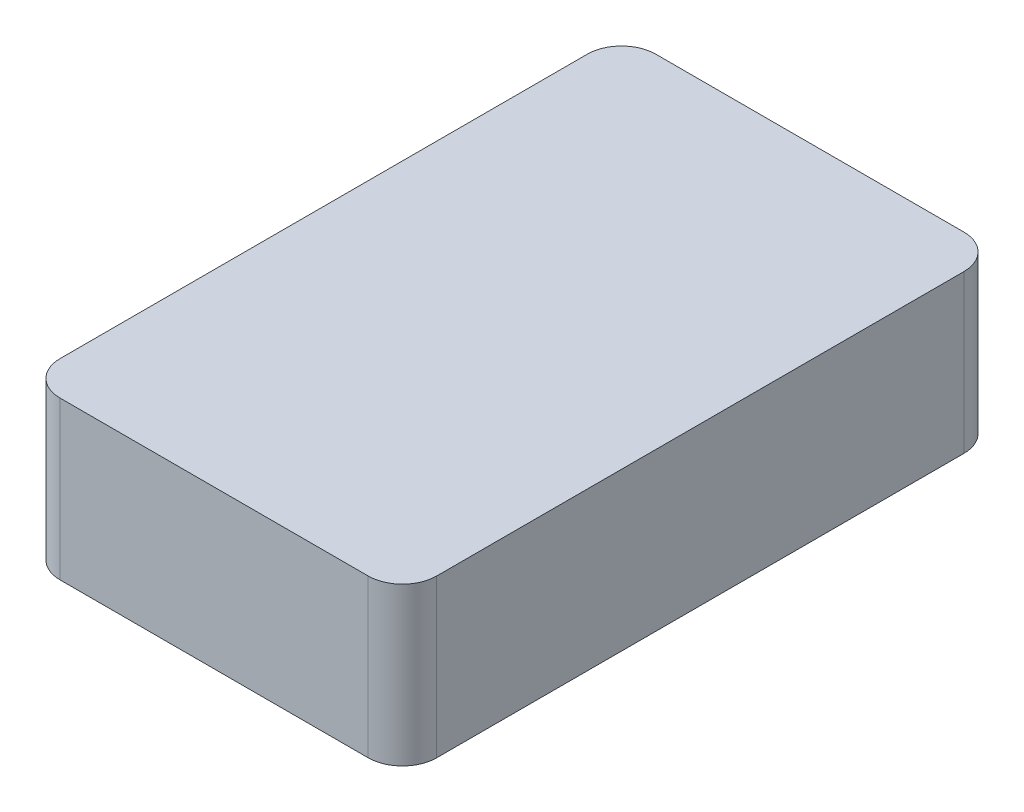
SolidWorks part; units mm, degrees
ref_plane "Front Plane" through (0, 0, 0) normal (0, 0, 1) x (1, 0, 0)
ref_plane "Top Plane" through (0, 0, 0) normal (0, 1, 0) x (1, 0, 0)
ref_plane "Right Plane" through (0, 0, 0) normal (1, 0, 0) x (0, 0, -1)
sketch "Sketch1" plane through (0, 0, 0) normal (0, 1, 0) x (1, 0, 0)
  line L1 (-34.9399, -25.7841) -> (10.0601, -25.7841)
  line L2 (-39.9399, -20.7841) -> (-39.9399, 56.2159)
  line L3 (-34.9399, 61.2159) -> (10.0601, 61.2159)
  line L4 (15.0601, -20.7841) -> (15.0601, 56.2159)
  arc A0 (-39.9399, -20.7841) -> (-34.9399, -25.7841) centre (-34.9399, -20.7841) ccw
  arc A1 (10.0601, 61.2159) -> (15.0601, 56.2159) centre (10.0601, 56.2159) cw
  arc A2 (-39.9399, 56.2159) -> (-34.9399, 61.2159) centre (-34.9399, 56.2159) cw
  arc A3 (10.0601, -25.7841) -> (15.0601, -20.7841) centre (10.0601, -20.7841) ccw
  dimension "D1" = 5
  dimension "D2" = 5
  dimension "D3" = 5
  dimension "D4" = 5
extrude "Boss-Extrude1" add sketch "Sketch1" along normal blind 23
